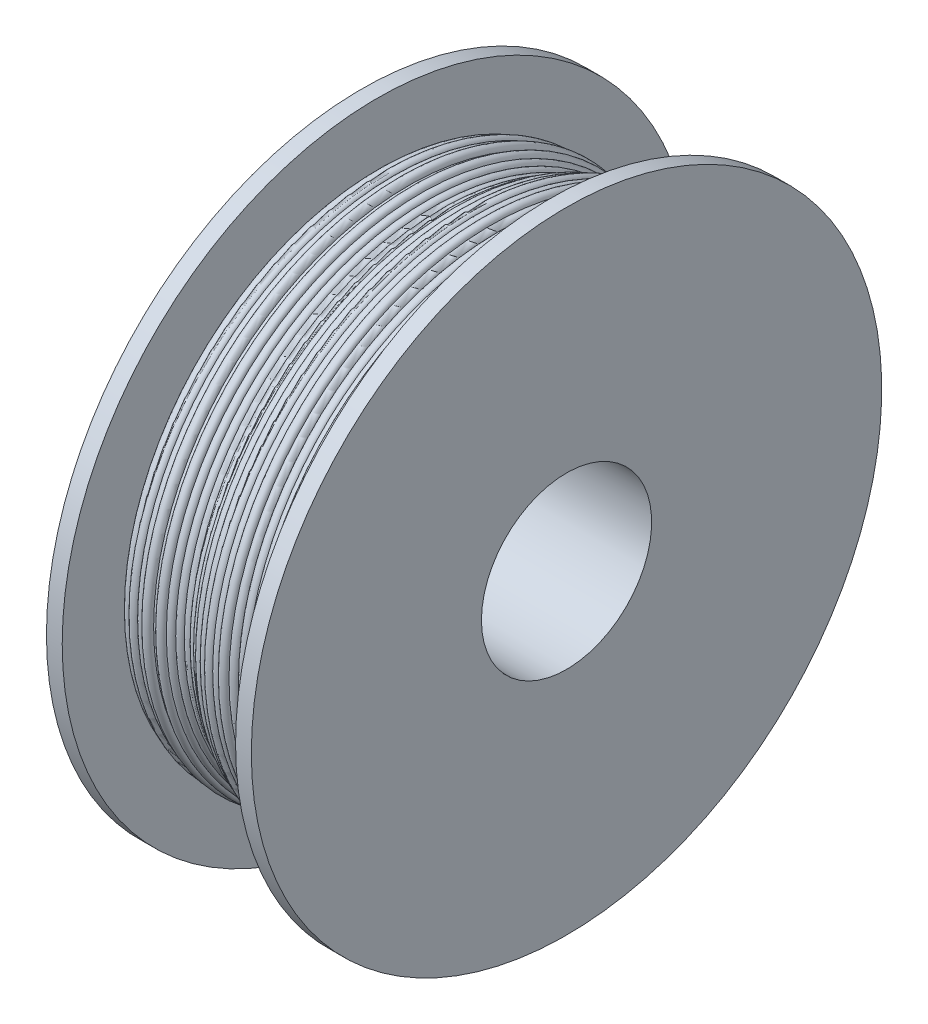
SolidWorks part; units mm, degrees
material "policarbonato"
ref_plane "Alzado" through (0, 0, 0) normal (0, 0, 1) x (1, 0, 0)
ref_plane "Planta" through (0, 0, 0) normal (0, 1, 0) x (1, 0, 0)
ref_plane "Vista lateral" through (0, 0, 0) normal (1, 0, 0) x (0, 0, -1)
sketch "Croquis1" plane through (0, 0, 0) normal (0, 0, 1) x (1, 0, 0)
  line L0 (-27.5, 0) -> (-27.5, 68)
  line L1 (-27.5, 68) -> (27.5, 68)
  line L2 (27.5, 68) -> (27.5, 0)
  line L3 (27.5, 0) -> (32.5, 0)
  line L4 (32.5, 0) -> (32.5, 73)
  line L5 (32.5, 73) -> (-32.5, 73)
  line L6 (-32.5, 73) -> (-32.5, 0)
  line L7 (-32.5, 0) -> (-27.5, 0)
  line L8 (-27.5, 0) -> (27.5, 0) construction
  line L9 (-54.879, 100) -> (50.3883, 100) construction
  dimension "D1" = 65
  dimension "D2" = 5
  dimension "D3" = 54
  dimension "D4" = 200
  dimension "D5" = 5
revolve "Revolución1" add sketch "Croquis1" angle 360 about L9
sketch "Croquis2" plane through (0, 0, 0) normal (0, 0, 1) x (1, 0, 0)
  line L0 (-27.5, 0) -> (-27.5, 200) construction
  line L1 (27.5, 200) -> (27.5, 0) construction
  line L2 (-27.5, 20.3439) -> (-27.5, 68)
  line L3 (-27.5, 68) -> (-27.5, 132) construction
  line L4 (-27.5, 68) -> (27.5, 68)
  line L5 (27.5, 68) -> (27.5, 19.1941)
  line L6 (-32.5, 100) -> (32.5, 100) construction
  line L7 (-32.5, 127) -> (-32.5, 73) construction
  line L8 (32.5, 0) -> (32.5, 200) construction
  arc A0 (-27.5, 20.3439) -> (-25.1279, 19.1235) centre (-26, 20.3439) ccw
  arc A1 (-25.1279, 19.1235) -> (-22.3294, 18.7514) centre (-23.6617, 19.4404) ccw
  arc A2 (-22.3294, 18.7514) -> (-20.5369, 18.4996) centre (-21.2668, 19.8101) ccw
  arc A3 (-20.5369, 18.4996) -> (-17.6206, 19.1227) centre (-19.1129, 18.971) ccw
  arc A4 (-17.6206, 19.1227) -> (-16.6713, 19.3362) centre (-17.4574, 20.6138) ccw
  arc A5 (-16.6713, 19.3362) -> (-13.6901, 19.2277) centre (-15.1749, 19.4404) ccw
  arc A6 (-13.6901, 19.2277) -> (-11.6775, 20.1914) centre (-13.1167, 20.6138) ccw
  arc A7 (-11.6775, 20.1914) -> (-9.6198, 20.8654) centre (-10.9718, 21.515) ccw
  arc A8 (-9.6198, 20.8654) -> (-7.7272, 20.9919) centre (-8.751, 22.0882) ccw
  arc A9 (-7.7272, 20.9919) -> (-5.5578, 20.2239) centre (-6.3214, 21.515) ccw
  arc A10 (-5.5578, 20.2239) -> (-3.5501, 18.9342) centre (-4.0626, 20.3439) ccw
  arc A11 (-3.5501, 18.9342) -> (-1.2088, 17.7295) centre (-2.0505, 18.971) ccw
  arc A12 (-1.2088, 17.7295) -> (1.1562, 17.0062) centre (0.222, 18.1798) ccw
  arc A13 (1.1562, 17.0062) -> (3.9281, 16.321) centre (2.6526, 17.1103) ccw
  arc A14 (3.9281, 16.321) -> (5.7712, 16.3105) centre (4.8564, 17.4992) ccw
  arc A15 (5.7712, 16.3105) -> (8.5247, 16.8954) centre (7.0402, 17.1103) ccw
  arc A16 (8.5247, 16.8954) -> (10.7207, 17.7) centre (9.2995, 18.1798) ccw
  arc A17 (10.7207, 17.7) -> (13.1484, 17.8464) centre (11.8817, 18.6498) ccw
  arc A18 (13.1484, 17.8464) -> (14.7877, 17.6176) centre (14.1411, 18.971) ccw
  arc A19 (14.7877, 17.6176) -> (17.5093, 17.0365) centre (16.2655, 17.8749) ccw
  arc A20 (17.5093, 17.0365) -> (20.1037, 17.2222) centre (18.7531, 17.8749) ccw
  arc A21 (20.1037, 17.2222) -> (22.4781, 17.7769) centre (21.0921, 18.3504) ccw
  arc A22 (22.4781, 17.7769) -> (24.7548, 18.3578) centre (23.3859, 18.971) ccw
  arc A23 (24.7548, 18.3578) -> (27.5, 19.1941) centre (26, 19.1941) ccw
  dimension "D1" = 3
revolve "Revolución2" add sketch "Croquis2" angle 360 about L6
